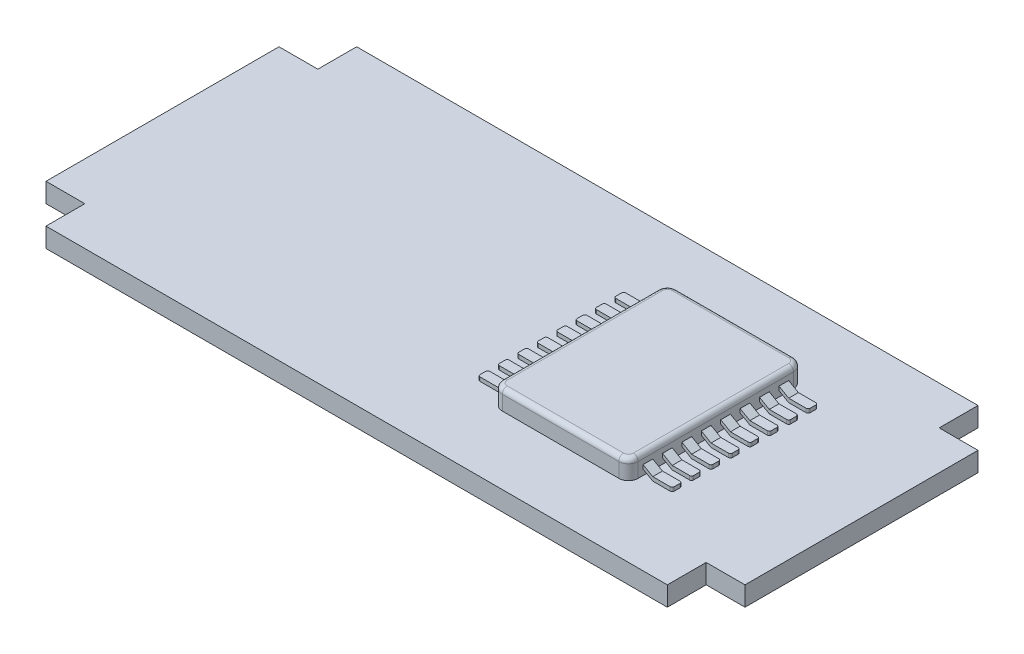
SolidWorks part; units mm, degrees
ref_plane "Piano frontale" through (0, 0, 0) normal (0, 0, 1) x (1, 0, 0)
ref_plane "Piano superiore" through (0, 0, 0) normal (0, 1, 0) x (1, 0, 0)
ref_plane "Piano destro" through (0, 0, 0) normal (1, 0, 0) x (0, 0, -1)
sketch "Schizzo1" plane through (0, 0, 0) normal (0, 1, 0) x (1, 0, 0)
  line L0 (-16, -8) -> (-16, -6)
  line L1 (-16, -8) -> (16, -8)
  line L2 (-18, -6) -> (-18, 6)
  line L3 (-16, 8) -> (16, 8)
  line L4 (18, -6) -> (18, 6)
  line L5 (0, 8) -> (0, -8) construction
  line L6 (-18, 0) -> (18, 0) construction
  line L7 (-16, -6) -> (-18, -6)
  line L8 (-18, 6) -> (-16, 6)
  line L9 (-16, 6) -> (-16, 8)
  line L11 (16, 8) -> (16, 6)
  line L12 (16, 6) -> (18, 6)
  line L14 (18, -6) -> (16, -6)
  line L15 (16, -6) -> (16, -8)
  point P0 (0, 0)
  point P13 (0, 0)
  dimension "D1" = 32
  dimension "D2" = 12
  dimension "D3" = 2
extrude "Estrusione-Estrusione1" add sketch "Schizzo1" along normal blind 1
sketch "Schizzo2" plane through (0, 1, 0) normal (0, 1, 0) x (1, 0, 0)
  line L1 (3.5, 4.5) -> (10.5, 4.5)
  line L2 (3.5, 4.5) -> (3.5, -4.5)
  line L3 (3.5, -4.5) -> (10.5, -4.5)
  line L4 (10.5, 4.5) -> (10.5, -4.5)
  line L5 (3.5, 4.5) -> (10.5, -4.5) construction
  line L6 (3.5, -4.5) -> (10.5, 4.5) construction
  point P0 (7, 0)
  dimension "D1" = 7
  dimension "D2" = 9
  dimension "D3" = 7
extrude "Estrusione-Estrusione2" add sketch "Schizzo2" along normal blind 1
fillet "Raccordo2" radius 0.5 4 edges at (3.5, 1.5, -4.5) (10.5, 1.5, -4.5) (10.5, 1.5, 4.5) (3.5, 1.5, 4.5)
fillet "Raccordo3" radius 0.25 8 edges at (10.3536, 2, -4.3536) (10.5, 2, 0) (10.3536, 2, 4.3536) (7, 2, 4.5) (3.6464, 2, 4.3536) (3.5, 2, 0) (3.6464, 2, -4.3536) (7, 2, -4.5)
sketch "Schizzo4" plane through (0, 1, 0) normal (0, 1, 0) x (1, 0, 0)
  line L0 (3.5, 4) -> (3.5, -4) construction
  line L1 (3, 4) -> (2, 4)
  line L2 (3, 4) -> (3, -4)
  line L3 (3, -4) -> (2, -4)
  line L4 (2, 4) -> (2, -4)
  dimension "D1" = 0.5
  dimension "D2" = 1
  dimension "D3" = 8
extrude "Estrusione-Estrusione6" add sketch "Schizzo4" along normal blind 0.2
sketch "Schizzo5" plane through (0, 0, 4) normal (0, 0, 1) x (1, 0, 0)
  line L0 (3, 1) -> (3, 1.2)
  line L1 (3, 1.2) -> (3.5, 1.4887)
  line L2 (3.5, 1) -> (3.5, 1.75) construction
  line L3 (3.5, 1.4887) -> (3.5, 1.2887)
  line L4 (3.5, 1.2887) -> (3, 1)
  line L5 (-16, 1) -> (16, 1) construction
  dimension "D1" = 30
extrude "Estrusione-Estrusione7" add sketch "Schizzo5" against normal blind 8
sketch "Schizzo6" plane through (0, 1, 0) normal (0, 1, 0) x (1, 0, 0)
  line L0 (3.5, 4) -> (3.5, -4) construction
  line L1 (3.5, -3.25) -> (2, -3.25)
  line L2 (3.5, -3.25) -> (3.5, -2.75)
  line L3 (3.5, -2.75) -> (2, -2.75)
  line L4 (2, -3.25) -> (2, -2.75)
  line L5 (2, 4) -> (2, -4) construction
  line L6 (2, 4) -> (2, -4) construction
  line L7 (3.5, -2.25) -> (2, -2.25)
  line L8 (3.5, -2.25) -> (3.5, -1.75)
  line L9 (3.5, -1.75) -> (2, -1.75)
  line L10 (2, -2.25) -> (2, -1.75)
  line L11 (3.5, -1.25) -> (2, -1.25)
  line L12 (3.5, -1.25) -> (3.5, -0.75)
  line L13 (3.5, -0.75) -> (2, -0.75)
  line L14 (2, -1.25) -> (2, -0.75)
  line L15 (3.5, -0.25) -> (2, -0.25)
  line L16 (3.5, -0.25) -> (3.5, 0.25)
  line L17 (3.5, 0.25) -> (2, 0.25)
  line L18 (2, -0.25) -> (2, 0.25)
  line L19 (11.8236, 0) -> (-7.2294, 0) construction
  line L20 (3.5, 0.75) -> (2, 0.75)
  line L21 (3.5, 0.75) -> (3.5, 1.25)
  line L22 (3.5, 1.25) -> (2, 1.25)
  line L23 (2, 0.75) -> (2, 1.25)
  line L24 (3.5, 1.75) -> (2, 1.75)
  line L25 (3.5, 1.75) -> (3.5, 2.25)
  line L26 (3.5, 2.25) -> (2, 2.25)
  line L27 (2, 1.75) -> (2, 2.25)
  line L28 (3.5, 2.75) -> (2, 2.75)
  line L29 (3.5, 2.75) -> (3.5, 3.25)
  line L30 (3.5, 3.25) -> (2, 3.25)
  line L31 (2, 2.75) -> (2, 3.25)
  line L32 (3.5, -4) -> (3.5, 4) construction
  line L33 (3.5, 3.75) -> (2, 3.75)
  line L34 (3.5, 3.75) -> (3.5, 4)
  line L35 (3.5, 4) -> (2, 4)
  line L36 (2, 3.75) -> (2, 4)
  line L38 (2, -4) -> (3.5, -4)
  line L39 (2, -4) -> (2, -3.75)
  line L40 (2, -3.75) -> (3.5, -3.75)
  line L41 (3.5, -4) -> (3.5, -3.75)
  dimension "D1" = 0.5
  dimension "D2" = 1.5
  dimension "D3" = 0.5
  dimension "D4" = 0.5
  dimension "D5" = 0.5
  dimension "D6" = 0.5
  dimension "D7" = 0.5
  dimension "D8" = 0.5
  dimension "D9" = 0.5
  dimension "D10" = 0.5
extrude "Taglio-Estrusione1" cut sketch "Schizzo6" along normal blind 1
fillet "Raccordo6" radius 0.1 16 edges at (2, 1.1, -3.75) (2, 1.1, -3.25) (2, 1.1, -2.75) (2, 1.1, -2.25) (2, 1.1, -1.75) (2, 1.1, -1.25) (2, 1.1, -0.75) (2, 1.1, -0.25) (2, 1.1, 0.25) (2, 1.1, 0.75) (2, 1.1, 1.25) (2, 1.1, 1.75) (2, 1.1, 2.25) (2, 1.1, 2.75) (2, 1.1, 3.25) (2, 1.1, 3.75)
sketch "Schizzo8" [suppressed] plane through (0, 2, 0) normal (0, 1, 0) x (1, 0, 0)
  line L0 (7, 5.6865) -> (7, -6.4538) construction
sketch "Schizzo9" [suppressed] plane through (0, 0, 4.5) normal (0, 0, 1) x (1, 0, 0)
  line L0 (7, 1) -> (7, 3.853) construction
  line L1 (4, 1) -> (10, 1) construction
ref_plane "Piano1" [suppressed] through (7, 0, 0) normal (-1, 0, 0) x (0, 0, 1)
mirror "Specchia1" about plane through (7, 0, 0) normal (-1, 0, 0) of "Raccordo6", "Taglio-Estrusione1", "Estrusione-Estrusione7", "Estrusione-Estrusione6"
